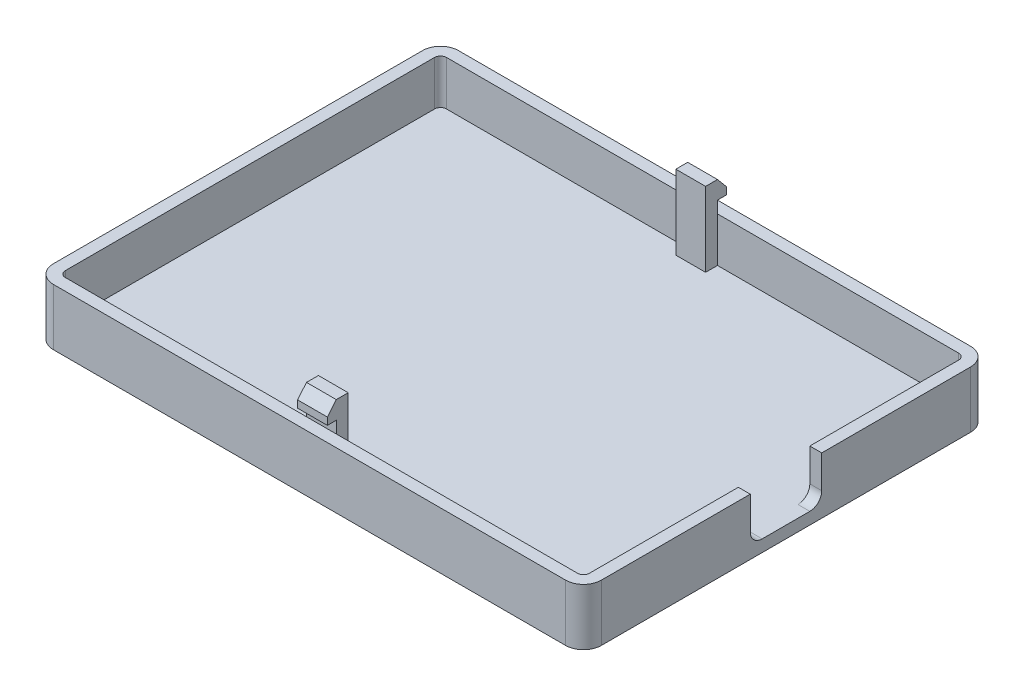
SolidWorks part; units mm, degrees
ref_plane "Front Plane" through (0, 0, 0) normal (0, 0, 1) x (1, 0, 0)
ref_plane "Top Plane" through (0, 0, 0) normal (0, 1, 0) x (1, 0, 0)
ref_plane "Right Plane" through (0, 0, 0) normal (1, 0, 0) x (0, 0, -1)
sketch "Sketch1" plane through (0, 0, 0) normal (0, 1, 0) x (1, 0, 0)
  line L1 (-46, 34) -> (46, 34)
  line L2 (-46, 34) -> (-46, -34)
  line L3 (-46, -34) -> (46, -34)
  line L4 (46, 34) -> (46, -34)
  line L5 (-46, 34) -> (46, -34) construction
  line L6 (-46, -34) -> (46, 34) construction
  point P0 (0, 0)
  dimension "D1" = 92
  dimension "D2" = 68
extrude "Boss-Extrude1" add sketch "Sketch1" along normal blind 9.5
fillet "Fillet1" radius 3 4 edges at (-46, 4.75, -34) (46, 4.75, -34) (46, 4.75, 34) (-46, 4.75, 34)
shell "Shell1" thickness 2
sketch "Sketch3" plane through (0, 2, 0) normal (0, 1, 0) x (1, 0, 0)
  line L0 (0, -55) -> (0, 55) construction
  line L1 (2.5, 30) -> (-2.5, 30)
  line L2 (2.5, 30) -> (2.5, 32)
  line L3 (2.5, 32) -> (-2.5, 32)
  line L4 (-2.5, 30) -> (-2.5, 32)
  line L5 (2.5, 30) -> (-2.5, 32) construction
  line L6 (2.5, 32) -> (-2.5, 30) construction
  line L7 (43, 32) -> (-43, 32) construction
  point P0 (0, 31)
  dimension "D2" = 2
  dimension "D3" = 5
extrude "Boss-Extrude2" add sketch "Sketch3" along normal blind 12.5
sketch "Sketch4" plane through (-2.5, 0, 0) normal (-1, 0, 0) x (0, 0, 1)
  line L0 (-32, 14.5) -> (-33.5, 12.7124)
  line L1 (-33.5, 12.7124) -> (-33.5, 11.5)
  line L2 (-33.5, 11.5) -> (-32, 11.5)
  line L3 (-32, 14.5) -> (-32, 9.5) construction
  line L4 (-32, 11.5) -> (-32, 14.5)
  dimension "D1" = 3
  dimension "D2" = 1.5
  dimension "D3" = 40
extrude "Boss-Extrude3" add sketch "Sketch4" against normal blind 5
mirror "Mirror1" about plane through (0, 0, 0) normal (0, 0, 1) of "Boss-Extrude3", "Boss-Extrude2"
sketch "Sketch5" plane through (46, 0, 0) normal (1, 0, 0) x (0, 0, -1)
  line L0 (0, 55) -> (0, -55) construction
  line L1 (-31, 9.5) -> (31, 9.5) construction
  line L2 (6, 2) -> (-6, 2)
  line L3 (6, 2) -> (6, 9.5)
  line L4 (6, 9.5) -> (-6, 9.5)
  line L5 (-6, 2) -> (-6, 9.5)
  line L6 (6, 2) -> (-6, 9.5) construction
  line L7 (6, 9.5) -> (-6, 2) construction
  point P2 (0, 5.75)
  dimension "D1" = 7.5
  dimension "D2" = 12
extrude "Cut-Extrude1" cut sketch "Sketch5" against normal up to next
fillet "Fillet2" radius 2 2 edges at (45, 2, -6) (45, 2, 6)
